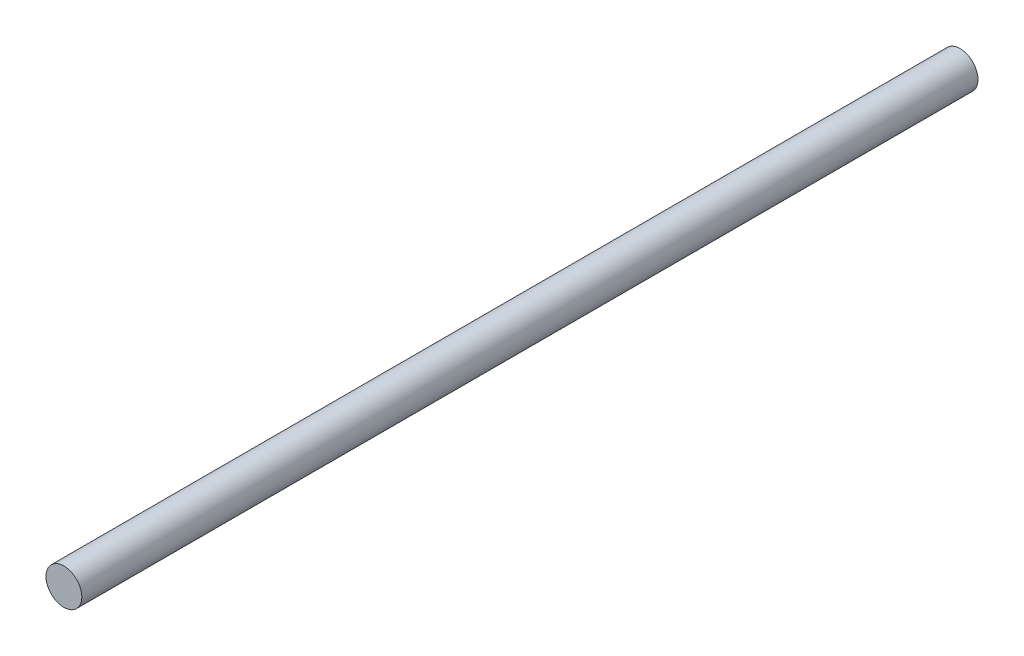
SolidWorks part; units mm, degrees
material "AISI Type A2 Tool Steel"
ref_plane "Front Plane" through (0, 0, 0) normal (0, 0, 1) x (1, 0, 0)
ref_plane "Top Plane" through (0, 0, 0) normal (0, 1, 0) x (1, 0, 0)
ref_plane "Right Plane" through (0, 0, 0) normal (1, 0, 0) x (0, 0, -1)
sketch "Sketch1" plane through (0, 0, 0) normal (0, 0, 1) x (1, 0, 0)
  line L0 (0, 2.5) -> (0, -2.5) construction
  circle A0 centre (0, 2.5) radius 1.5
  point P2 (0, 0)
  dimension "D1" = 3
  dimension "D2" = 5
extrude "Boss-Extrude1" add sketch "Sketch1" along normal blind 75
